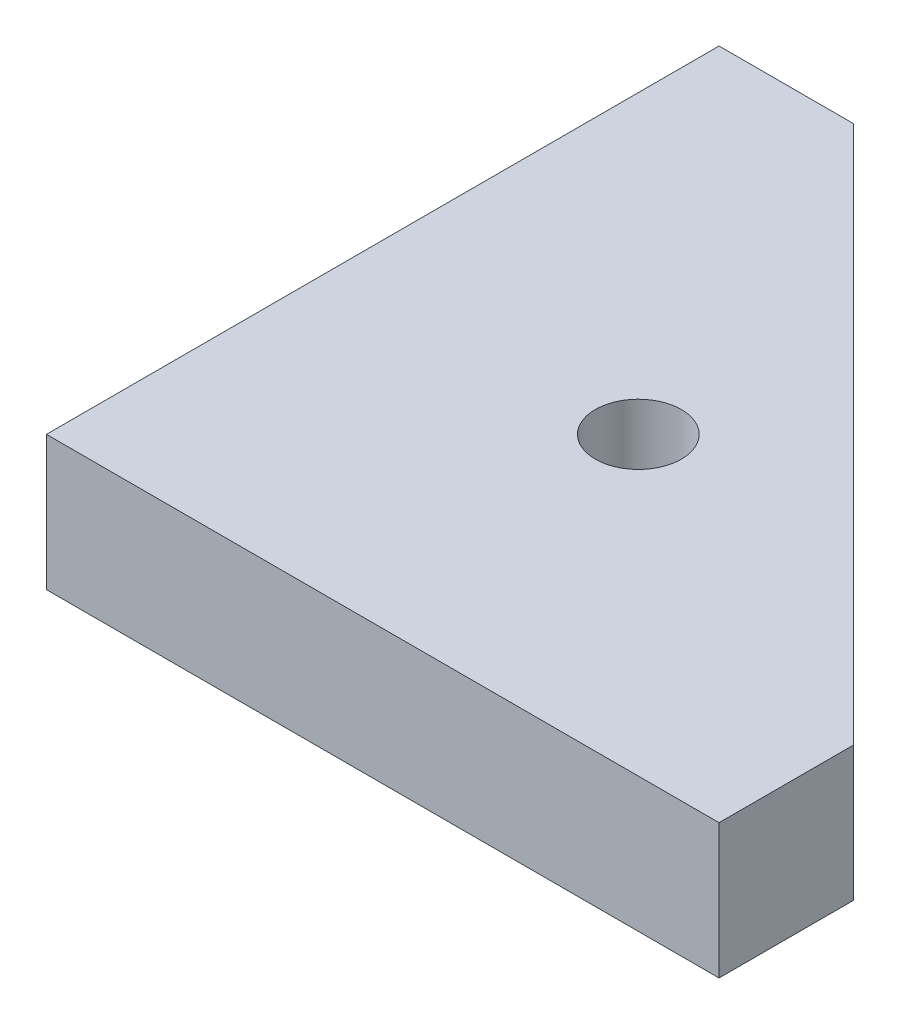
SolidWorks part; units mm, degrees
ref_plane "正面" through (0, 0, 0) normal (0, 0, 1) x (1, 0, 0)
ref_plane "平面" through (0, 0, 0) normal (0, 1, 0) x (1, 0, 0)
ref_plane "右側面" through (0, 0, 0) normal (1, 0, 0) x (0, 0, -1)
sketch "ｽｹｯﾁ1" plane through (0, 0, 0) normal (0, 1, 0) x (1, 0, 0)
  line L0 (5, 25) -> (25, 5)
  line L1 (0, 0) -> (25, 0)
  line L2 (0, 0) -> (0, 25)
  line L3 (0, 25) -> (25, 25)
  line L4 (25, 0) -> (25, 25)
  circle A0 centre (11, 11) radius 1.6
  dimension "D5" = 3.2
  dimension "D1" = 25
  dimension "D2" = 25
  dimension "D3" = 5
  dimension "D4" = 5
  dimension "D6" = 11
  dimension "D7" = 11
extrude "ﾎﾞｽ - 押し出し1" add sketch "ｽｹｯﾁ1" along normal blind 5 contours L1 L4 L0 L3 L2 A0
